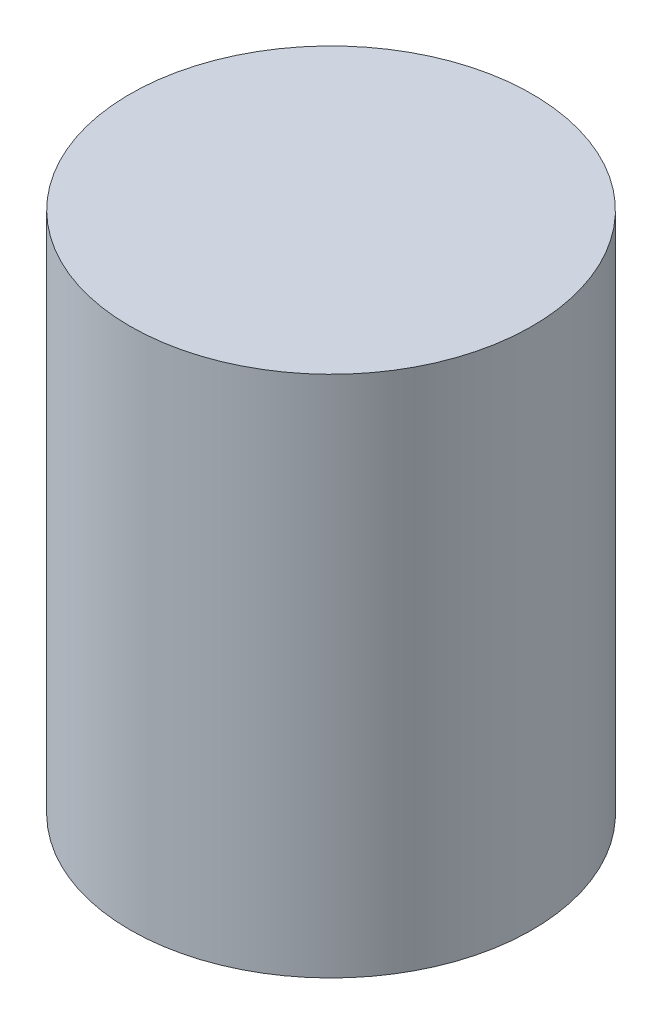
SolidWorks part; units mm, degrees
ref_plane "Front Plane" through (0, 0, 0) normal (0, 0, 1) x (1, 0, 0)
ref_plane "Top Plane" through (0, 0, 0) normal (0, 1, 0) x (1, 0, 0)
ref_plane "Right Plane" through (0, 0, 0) normal (1, 0, 0) x (0, 0, -1)
sketch "Sketch1" plane through (0, 34.902, 0) normal (0, 1, 0) x (1, 0, 0)
  circle A0 centre (-13.6798, -47.7982) radius 15
  dimension "D1" = 30
extrude "Boss-Extrude1" add sketch "Sketch1" against normal blind 39
